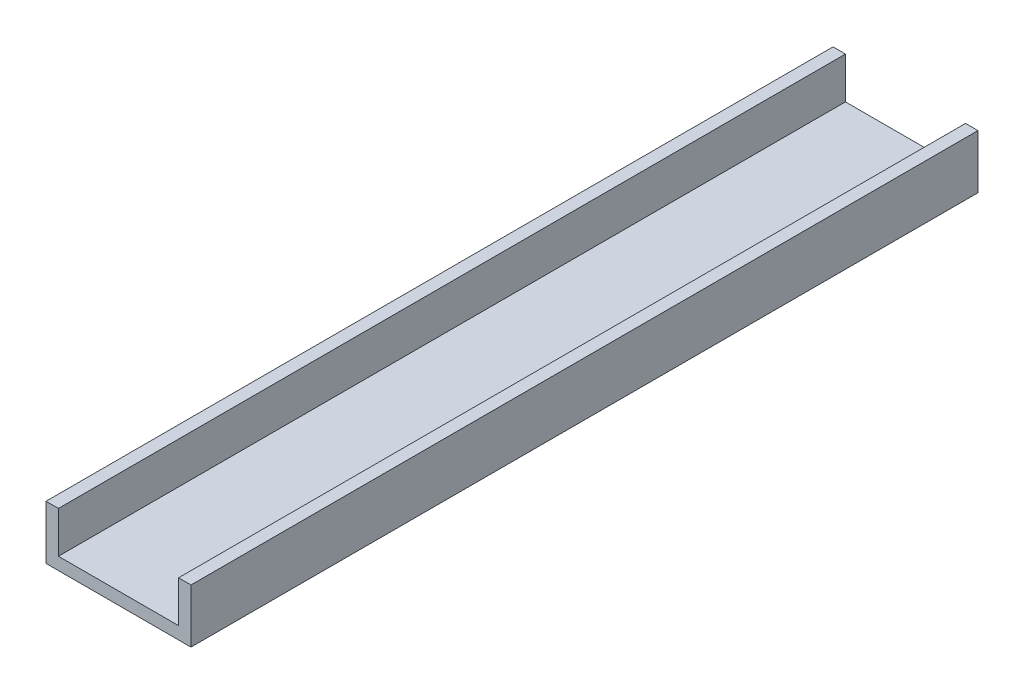
SolidWorks part; units mm, degrees
ref_plane "Front Plane" through (0, 0, 0) normal (0, 0, 1) x (1, 0, 0)
ref_plane "Top Plane" through (0, 0, 0) normal (0, 1, 0) x (1, 0, 0)
ref_plane "Right Plane" through (0, 0, 0) normal (1, 0, 0) x (0, 0, -1)
sketch "Sketch1" plane through (0, 0, 0) normal (0, 1, 0) x (1, 0, 0)
  line L1 (0, 0) -> (35, 0)
  line L2 (0, 0) -> (0, -190)
  line L3 (0, -190) -> (35, -190)
  line L4 (35, 0) -> (35, -190)
  dimension "D1" = 35
  dimension "D2" = 190
extrude "Boss-Extrude1" add sketch "Sketch1" along normal blind 3
sketch "Sketch2" plane through (0, 3, 0) normal (0, 1, 0) x (1, 0, 0)
  line L6 (32, 0) -> (32, -190)
  line L9 (35, 0) -> (35, -190)
  line L10 (0, 0) -> (0, -190) construction
  line L12 (32, 0) -> (35, 0)
  line L22 (0, 0) -> (3, 0)
  line L23 (0, 0) -> (0, -190)
  line L24 (0, -190) -> (3, -190)
  line L25 (3, 0) -> (3, -190)
  line L26 (32, -190) -> (35, -190)
  line L27 (35, 0) -> (0, 0) construction
  line L28 (35, -190) -> (35, 0) construction
  dimension "D1" = 3
  dimension "D2" = 3
extrude "Boss-Extrude2" add sketch "Sketch2" along normal blind 10
